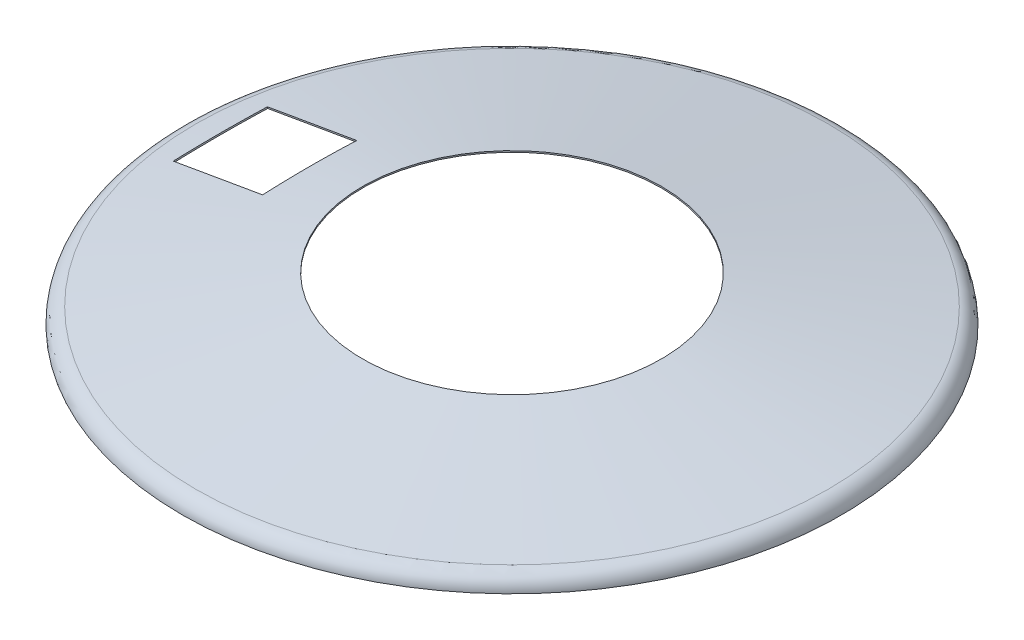
SolidWorks part; units mm, degrees
material "AISI 304"
ref_plane "Спереди" through (0, 0, 0) normal (0, 0, 1) x (1, 0, 0)
ref_plane "Сверху" through (0, 0, 0) normal (0, 1, 0) x (1, 0, 0)
ref_plane "Справа" through (0, 0, 0) normal (1, 0, 0) x (0, 0, -1)
sketch "Эскиз1" plane through (0, 0, 0) normal (0, 0, 1) x (1, 0, 0)
  line L0 (0, 73.5048) -> (0, 0) construction
  line L1 (0, 0) -> (-700, 0) construction
  line L2 (-671.8945, 33.4851) -> (-10, 150)
  line L3 (-671.3744, 30.5306) -> (-9.4799, 147.0454)
  line L4 (-10, 150) -> (-9.4799, 147.0454)
  line L5 (-700, 0) -> (-697, 0)
  arc A0 (-700, 0) -> (-671.8945, 33.4851) centre (-666, 0) cw
  arc A1 (-697, 0) -> (-671.3744, 30.5306) centre (-666, 0) cw
  dimension "D4" = 34
  dimension "D1" = 150
  dimension "D2" = 20
  dimension "D3" = 1400
  dimension "D5" = 3
revolve "Повернуть1" add sketch "Эскиз1" angle 360 about L0
sketch "Эскиз2" plane through (0, 0, 0) normal (0, 1, 0) x (1, 0, 0)
  circle A0 centre (0, 0) radius 317.5
  dimension "D1" = 635
extrude "Вырез-Вытянуть2" cut sketch "Эскиз2" along normal through all
sketch3d "Трехмерный эскиз1"
  line L0 (-466.8334, 217.7, -135) -> (-466.8334, 217.7, 135)
  line L1 (-692, 87.7, -135) -> (-692, 87.7, 135)
  line L8 (-656.926, 107.95, -95.5) -> (-656.926, 107.95, 95.5)
  line L9 (-579.4167, 152.7, -99.5) -> (-653.4619, 109.95, -99.5)
  line L10 (-653.4619, 109.95, 99.5) -> (-579.4167, 152.7, 99.5)
  line L11 (-505.3715, 195.45, 99.5) -> (-579.4167, 152.7, 99.5)
  line L12 (-501.9074, 197.45, -95.5) -> (-501.9074, 197.45, 95.5)
  line L13 (-579.4167, 152.7, -99.5) -> (-505.3715, 195.45, -99.5)
  arc A4 (-653.4619, 109.95, -99.5) -> (-656.926, 107.95, -95.5) centre (-653.4619, 109.95, -95.5) ccw
  arc A5 (-656.926, 107.95, 95.5) -> (-653.4619, 109.95, 99.5) centre (-653.4619, 109.95, 95.5) ccw
  arc A6 (-501.9074, 197.45, 95.5) -> (-505.3715, 195.45, 99.5) centre (-505.3715, 195.45, 95.5) ccw
  arc A7 (-505.3715, 195.45, -99.5) -> (-501.9074, 197.45, -95.5) centre (-505.3715, 195.45, -95.5) ccw
  point P21 (-655.4619, 113.4141, -95.5)
  point P23 (-655.4619, 113.4141, 95.5)
  point P24 (-503.3715, 191.9859, 95.5)
  point P25 (-503.3715, 191.9859, -95.5)
ref_plane "Плоскость1" through (-210.9752, 365.4198, 0) normal (0.5, -0.866, 0) x (-0.866, -0.5, 0)
sketch "Эскиз3" plane through (-210.9752, 365.4198, 0) normal (0.5, -0.866, 0) x (-0.866, -0.5, 0)
  line L0 (335.9396, 95.5) -> (335.9396, -95.5) construction
  line L1 (425.4396, 99.5) -> (339.9396, 99.5) construction
  line L2 (425.4396, 99.5) -> (510.9396, 99.5) construction
  line L3 (514.9396, 95.5) -> (514.9396, -95.5) construction
  line L4 (510.9396, -99.5) -> (425.4396, -99.5) construction
  line L5 (339.9396, -99.5) -> (425.4396, -99.5) construction
  line L6 (335.9396, 95.5) -> (335.9396, -95.5)
  line L7 (425.4396, 99.5) -> (339.9396, 99.5)
  line L8 (425.4396, 99.5) -> (510.9396, 99.5)
  line L9 (514.9396, 95.5) -> (514.9396, -95.5)
  line L10 (510.9396, -99.5) -> (425.4396, -99.5)
  line L11 (339.9396, -99.5) -> (425.4396, -99.5)
  arc A0 (339.9396, 99.5) -> (335.9396, 95.5) centre (339.9396, 95.5) ccw construction
  arc A1 (514.9396, 95.5) -> (510.9396, 99.5) centre (510.9396, 95.5) ccw construction
  arc A2 (510.9396, -99.5) -> (514.9396, -95.5) centre (510.9396, -95.5) ccw construction
  arc A3 (335.9396, -95.5) -> (339.9396, -99.5) centre (339.9396, -95.5) ccw construction
  arc A4 (339.9396, 99.5) -> (335.9396, 95.5) centre (339.9396, 95.5) ccw
  arc A5 (514.9396, 95.5) -> (510.9396, 99.5) centre (510.9396, 95.5) ccw
  arc A6 (510.9396, -99.5) -> (514.9396, -95.5) centre (510.9396, -95.5) ccw
  arc A7 (335.9396, -95.5) -> (339.9396, -99.5) centre (339.9396, -95.5) ccw
extrude "Вырез-Вытянуть3" cut sketch "Эскиз3" along normal through all
ref_plane "Плоскость2" through (-25.9118, 147.199, 0) normal (-0.1734, 0.9849, 0) x (0.9849, 0.1734, 0)
sketch "Эскиз4" plane through (-25.9118, 147.199, 0) normal (-0.1734, 0.9849, 0) x (0.9849, 0.1734, 0)
  line L0 (-602.9925, 0) -> (-602.4925, 0) construction
  line L1 (-602.9925, 100) -> (-410.3919, 100)
  line L2 (-602.9925, 100) -> (-602.9925, -100)
  line L3 (-602.9925, -100) -> (-410.3919, -100)
  line L4 (-410.3919, 100) -> (-410.3919, -100)
  line L5 (-597.7297, 99.5) -> (-415.5321, 99.5) construction
  line L6 (-415.5321, -99.5) -> (-597.7297, -99.5) construction
  line L7 (-410.3919, 0) -> (-410.8919, 0) construction
  spline S3 degree 3 poles (-602.0296, -95.5) (-602.3367, -63.6667) (-602.6482, 0) (-602.3367, 63.6667) (-602.0296, 95.5) knots 0 0 0 0 0.5 1 1 1 1 construction
  spline S4 degree 3 poles (-410.2289, -95.5) (-410.4477, -79.5833) (-410.6139, -63.6667) (-410.836, -31.8333) (-410.9479, 0) (-410.836, 31.8333) (-410.6139, 63.6667) (-410.4477, 79.5833) (-410.2289, 95.5) knots 0 0 0 0 0.25 0.25 0.5 0.75 0.75 1 1 1 1 construction
  dimension "D1" = 0.5
  dimension "D2" = 0.5
  dimension "D3" = 0.5
  dimension "D4" = 0.5
extrude "Вырез-Вытянуть4" cut sketch "Эскиз4" against normal blind 5
